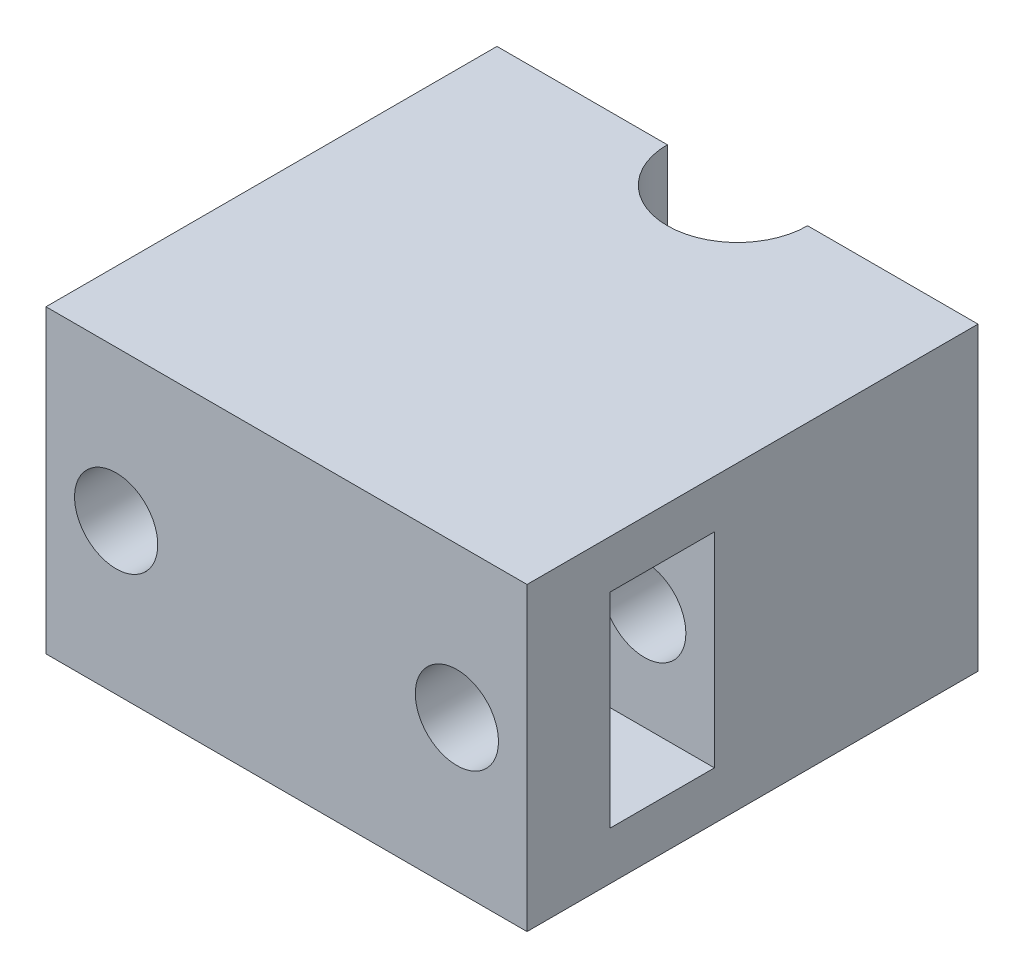
SolidWorks part; units mm, degrees
ref_plane "Спереди" through (0, 0, 0) normal (0, 0, 1) x (1, 0, 0)
ref_plane "Сверху" through (0, 0, 0) normal (0, 1, 0) x (1, 0, 0)
ref_plane "Справа" through (0, 0, 0) normal (1, 0, 0) x (0, 0, -1)
sketch "Sketch1" plane through (0, 0, 0) normal (0, 1, 0) x (1, 0, 0)
  line L1 (24, -22.5) -> (-24, -22.5)
  line L2 (24, -22.5) -> (24, 22.5)
  line L3 (24, 22.5) -> (-24, 22.5)
  line L4 (-24, -22.5) -> (-24, 22.5)
  line L5 (24, -22.5) -> (-24, 22.5) construction
  line L6 (24, 22.5) -> (-24, -22.5) construction
  point P0 (0, 0)
  dimension "D1" = 48
  dimension "D2" = 45
extrude "Boss-Extrude1" add sketch "Sketch1" along normal blind 30
sketch "Sketch2" plane through (24, 0, 0) normal (1, 0, 0) x (0, 0, -1)
  line L0 (-22.5, 15) -> (22.5, 15) construction
  line L1 (-22.5, 30) -> (-22.5, 0) construction
  line L2 (22.5, 30) -> (22.5, 0) construction
  line L4 (-14.2, 4.8) -> (-3.8, 4.8)
  line L5 (-14.2, 4.8) -> (-14.2, 25.2)
  line L6 (-14.2, 25.2) -> (-3.8, 25.2)
  line L7 (-3.8, 4.8) -> (-3.8, 25.2)
  line L8 (-14.2, 4.8) -> (-3.8, 25.2) construction
  line L9 (-14.2, 25.2) -> (-3.8, 4.8) construction
  point P6 (-9, 15)
  dimension "D1" = 10.4
  dimension "D2" = 20.4
  dimension "D3" = 31.5
extrude "Cut-Extrude1" cut sketch "Sketch2" against normal offset from surface (45 mm away) 3 up to face at (-24, 15, 0)
sketch "Sketch3" plane through (0, 0, 22.5) normal (0, 0, 1) x (1, 0, 0)
  line L0 (-24, 15) -> (24, 15) construction
  line L1 (-24, 30) -> (-24, 0) construction
  line L2 (24, 30) -> (24, 0) construction
  circle A0 centre (-17, 15) radius 4.15
  circle A1 centre (17, 15) radius 4.15
  point P10 (0, 15)
  dimension "D1" = 34
  dimension "D2" = 8.3
  dimension "D3" = 17
extrude "Cut-Extrude2" cut sketch "Sketch3" against normal through all
sketch "Sketch4" plane through (0, 30, 0) normal (0, 1, 0) x (1, 0, 0)
  line L0 (0, 22.5) -> (0, -22.5) construction
  line L1 (24, 22.5) -> (-24, 22.5) construction
  line L2 (-24, -22.5) -> (24, -22.5) construction
  arc A0 (-7, 22.5) -> (7, 22.5) centre (0, 22.5) ccw
  dimension "D1" = 7
extrude "Cut-Extrude3" cut sketch "Sketch4" against normal through all and the other way through all
